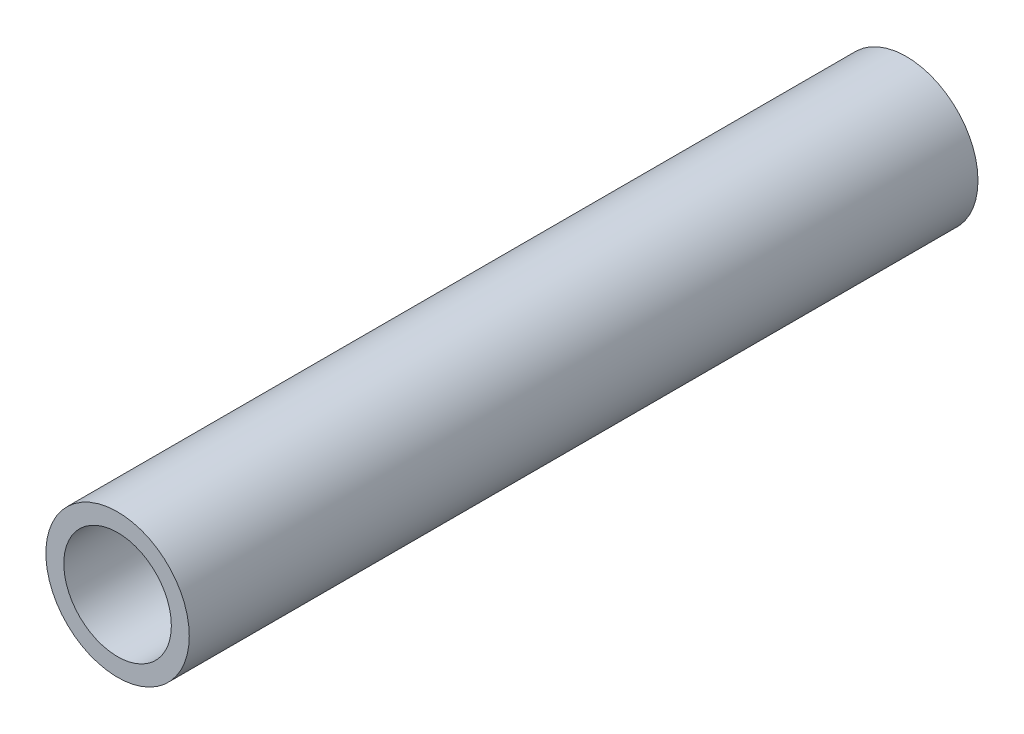
SolidWorks part; units mm, degrees
ref_plane "Front Plane" through (0, 0, 0) normal (1, 0, 0) x (0, 1, 0)
ref_plane "Top Plane" through (0, 0, 0) normal (0, 0, 1) x (0, 1, 0)
ref_plane "Right Plane" through (0, 0, 0) normal (0, 1, 0) x (-1, 0, 0)
sketch "Sketch2" plane through (0, 0, 0) normal (0, 0, 1) x (0, 1, 0)
  circle A0 centre (0, 0) radius 4.7625
  circle A1 centre (0, 0) radius 6.35
  dimension "D1" = 9.525
  dimension "D2" = 12.7
extrude "Boss-Extrude1" add sketch "Sketch2" along normal mid plane 69.85
